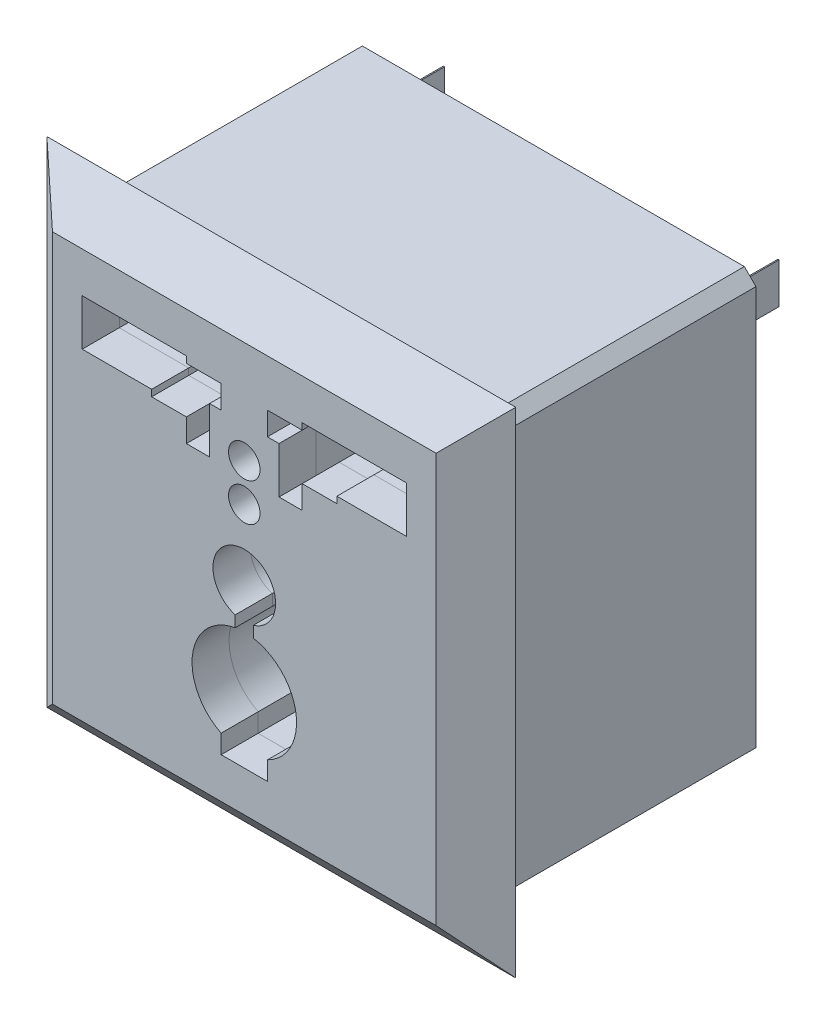
SolidWorks part; units mm, degrees
ref_plane "Front Plane" through (0, 0, 0) normal (0, 0, 1) x (1, 0, 0)
ref_plane "Top Plane" through (0, 0, 0) normal (0, 1, 0) x (1, 0, 0)
ref_plane "Right Plane" through (0, 0, 0) normal (1, 0, 0) x (0, 0, -1)
sketch "Sketch1" plane through (0, 0, 0) normal (0, 0, 1) x (1, 0, 0)
  line L1 (-20.25, 21.35) -> (20.25, 21.35)
  line L2 (-20.25, 21.35) -> (-20.25, -21.35)
  line L3 (-20.25, -21.35) -> (20.25, -21.35)
  line L4 (20.25, 21.35) -> (20.25, -21.35)
  line L5 (-20.25, 21.35) -> (20.25, -21.35) construction
  line L6 (-20.25, -21.35) -> (20.25, 21.35) construction
  point P0 (0, 0)
  dimension "D1" = 42.7
  dimension "D2" = 40.5
sketch "Sketch2" plane through (0, 0, 0) normal (0, 0, 1) x (1, 0, 0)
extrude "Boss-Extrude1" add sketch "Sketch1" along normal blind 3.2 draft 49 contours L1 L4 L3 L2
sketch "Sketch6" plane through (0, 0, 0) normal (0, 0, -1) x (-1, 0, 0)
  line L0 (0.05, -20) -> (-0.05, -20)
  line L1 (-17.5, 18.25) -> (17.5, 18.25)
  line L2 (-17.5, 18.25) -> (-17.5, -18.25)
  line L3 (-17.5, -18.25) -> (17.5, -18.25)
  line L4 (17.5, 18.25) -> (17.5, -18.25)
  line L5 (-17.5, 18.25) -> (17.5, -18.25) construction
  line L6 (-17.5, -18.25) -> (17.5, 18.25) construction
  line L7 (1.75, -14.5256) -> (-1.75, -14.5256)
  line L8 (1.75, -14.5256) -> (1.75, -14.4256)
  line L9 (1.75, -14.4256) -> (-1.75, -14.4256)
  line L10 (-1.75, -14.5256) -> (-1.75, -14.4256)
  line L11 (1.75, -14.5256) -> (-1.75, -14.4256) construction
  line L12 (1.75, -14.4256) -> (-1.75, -14.5256) construction
  line L17 (0.05, -20) -> (0.05, -16.5)
  line L18 (0.05, -16.5) -> (-0.05, -16.5)
  line L19 (14.5, 11.75) -> (14.4, 11.75)
  line L20 (14.5, 11.75) -> (14.5, 15.25)
  line L21 (14.5, 15.25) -> (14.4, 15.25)
  line L22 (14.4, 11.75) -> (14.4, 15.25)
  line L23 (14.5, 11.75) -> (14.4, 15.25) construction
  line L24 (14.5, 15.25) -> (14.4, 11.75) construction
  line L25 (-0.05, -20) -> (-0.05, -16.5)
  point P0 (0, 0)
  point P6 (0, -14.4756)
  point P16 (14.45, 13.5)
  dimension "D1" = 36.5
  dimension "D2" = 35
  dimension "D3" = 3.5
  dimension "D4" = 0.1
  dimension "D5" = 17.5
  dimension "D9" = 3.5
  dimension "D10" = 0.1
  dimension "D11" = 3
  dimension "D12" = 3
extrude "Boss-Extrude2" add sketch "Sketch6" along normal blind 23.5 contours L2 L1 L4 L3
sketch "Sketch7" plane through (0, 0, -23.5) normal (0, 0, -1) x (-1, 0, 0)
  line L0 (-17.5, 18.25) -> (-16.5, 18.25)
  line L1 (-16.5, 18.25) -> (-17.5, 17.25)
  line L2 (-17.5, 17.25) -> (-17.5, 18.25)
  line L3 (-17.5, 18.25) -> (17.5, 18.25) construction
  line L4 (-17.5, 18.25) -> (-17.5, -18.25) construction
  line L5 (17.5, 18.25) -> (17.5, 17.25)
  line L6 (17.5, 18.25) -> (17.5, -18.25) construction
  line L7 (17.5, 17.25) -> (16.5, 18.25)
  line L8 (16.5, 18.25) -> (17.5, 18.25)
  line L9 (17.5, -18.25) -> (17.5, -17.25)
  line L10 (17.5, -17.25) -> (16.5, -18.25)
  line L11 (-17.5, -18.25) -> (17.5, -18.25) construction
  line L12 (16.5, -18.25) -> (17.5, -18.25)
  line L13 (-17.5, -18.25) -> (-16.5, -18.25)
  line L14 (-16.5, -18.25) -> (-17.5, -17.25)
  line L15 (-17.5, -17.25) -> (-17.5, -18.25)
  dimension "D1" = 1
  dimension "D2" = 1
  dimension "D3" = 1
  dimension "D4" = 1
  dimension "D5" = 1
  dimension "D6" = 1
  dimension "D7" = 1
  dimension "D8" = 1
sketch "Sketch10" plane through (0, 0, -23.5) normal (0, 0, -1) x (-1, 0, 0)
sketch "Sketch11" plane through (0, 0, -23.5) normal (0, 0, -1) x (-1, 0, 0)
sketch "Sketch9" plane through (0, 0, 3.2) normal (0, 0, 1) x (1, 0, 0)
  line L0 (-16.5688, -17.6688) -> (16.5688, -17.6688) construction
  line L1 (2.0012, -14.1688) -> (-1.9988, -14.1688)
  line L2 (2.0012, -14.1688) -> (2.0012, -8.507)
  line L3 (2.0012, -8.507) -> (-1.9988, -8.507)
  line L4 (-1.9988, -14.1688) -> (-1.9988, -8.507)
  line L5 (2.0012, -14.1688) -> (-1.9988, -8.507) construction
  line L6 (2.0012, -8.507) -> (-1.9988, -14.1688) construction
  line L7 (0.7841, -5.6938) -> (-0.7817, -5.6938)
  line L8 (0.7841, -5.6938) -> (0.7841, -2.2911)
  line L9 (0.7841, -2.2911) -> (-0.7817, -2.2911)
  line L10 (-0.7817, -5.6938) -> (-0.7817, -2.2911)
  line L11 (0.7841, -5.6938) -> (-0.7817, -2.2911) construction
  line L12 (0.7841, -2.2911) -> (-0.7817, -5.6938) construction
  line L13 (-3, 7.6044) -> (-5, 7.6044)
  line L14 (-3, 7.6044) -> (-3, 11.6044)
  line L15 (-3, 11.6044) -> (-5, 11.6044)
  line L16 (-5, 7.6044) -> (-5, 11.6044)
  line L17 (-5, 11.6044) -> (-2, 11.6044)
  line L18 (-5, 11.6044) -> (-5, 13.6044)
  line L19 (-5, 13.6044) -> (-2, 13.6044)
  line L20 (-2, 11.6044) -> (-2, 13.6044)
  line L21 (-5, 9.6044) -> (-8, 9.6044)
  line L22 (-5, 9.6044) -> (-5, 11.6044)
  line L23 (-5, 11.6044) -> (-8, 11.6044)
  line L24 (-8, 9.6044) -> (-8, 11.6044)
  line L25 (-5, 10.1688) -> (-14, 10.1688)
  line L26 (-5, 10.1688) -> (-5, 14.1688)
  line L27 (-5, 14.1688) -> (-14, 14.1688)
  line L28 (-14, 10.1688) -> (-14, 14.1688)
  line L29 (-16.5688, 17.6688) -> (16.5688, 17.6688) construction
  line L62 (-16.5688, 17.6688) -> (-16.5688, -17.6688) construction
  line L63 (14, 10.1688) -> (5, 10.1688)
  line L64 (14, 10.1688) -> (14, 14.1688)
  line L65 (14, 14.1688) -> (5, 14.1688)
  line L66 (5, 10.1688) -> (5, 14.1688)
  line L67 (2, 11.6088) -> (5, 11.6088)
  line L68 (2, 11.6088) -> (2, 13.6088)
  line L69 (2, 13.6088) -> (5, 13.6088)
  line L70 (5, 11.6088) -> (5, 13.6088)
  line L71 (5, 7.6088) -> (3, 7.6088)
  line L72 (5, 7.6088) -> (5, 11.6088)
  line L73 (5, 11.6088) -> (3, 11.6088)
  line L74 (3, 7.6088) -> (3, 11.6088)
  line L75 (8, 9.6088) -> (5, 9.6088)
  line L76 (8, 9.6088) -> (8, 11.6088)
  line L77 (8, 11.6088) -> (5, 11.6088)
  line L78 (5, 9.6088) -> (5, 11.6088)
  line L79 (16.5688, 17.6688) -> (16.5688, -17.6688) construction
  circle A0 centre (0.0012, -8.507) radius 4.5146
  circle A1 centre (0.0012, -0.5054) radius 2.7059
  circle A2 centre (0, 5.5548) radius 1.36
  circle A3 centre (0, 8.8223) radius 1.36
  point P0 (0.0012, -11.3379)
  point P5 (0.0012, -3.9924)
  point P34 (0, -17.6688)
  point P61 (0.0012, -2.2911)
  dimension "D28" = 9.0292
  dimension "D30" = 5.4118
  dimension "D31" = 2.72
  dimension "D32" = 2.72
  dimension "D1" = 3.5
  dimension "D2" = 3.5
  dimension "D3" = 3
  dimension "D4" = 6
  dimension "D5" = 12
  dimension "D6" = 2
  dimension "D7" = 3.5
  dimension "D8" = 0.56
  dimension "D9" = 2
  dimension "D10" = 2
  dimension "D11" = 9
  dimension "D12" = 16.5688
  dimension "D13" = 2
  dimension "D14" = 4
  dimension "D15" = 4
  dimension "D16" = 2
  dimension "D17" = 12
  dimension "D18" = 4
  dimension "D19" = 2
  dimension "D20" = 3
  dimension "D21" = 0.5644
  dimension "D22" = 5
  dimension "D23" = 16.57
  dimension "D24" = 4
  dimension "D25" = 5.6618
  dimension "D26" = 16.57
  dimension "D27" = 1.5658
  dimension "D29" = 3.4027
  dimension "D33" = 6.0602
  dimension "D34" = 3.2675
  dimension "D35" = 4
  dimension "D36" = 2
  dimension "D37" = 1.7856
  dimension "D38" = 16.5688
  dimension "D39" = 2
  dimension "D40" = 3
  dimension "D41" = 2
  dimension "D42" = 3
extrude "Cut-Extrude9" cut sketch "Sketch7" against normal up to next (23.5 mm away)
sketch "Sketch13" plane through (0, 0, -23.5) normal (0, 0, -1) x (-1, 0, 0)
  line L12 (-16.5, 18.25) -> (16.5, 18.25) construction
  line L13 (-14.5, 15.25) -> (-14.4, 15.25)
  line L17 (-14.5, 15.25) -> (-14.5, 11.75)
  line L18 (-14.5, 11.75) -> (-14.4, 11.75)
  line L19 (-14.4, 15.25) -> (-14.4, 11.75)
  line L20 (-14.5, 15.25) -> (-14.4, 11.75) construction
  line L21 (-14.5, 11.75) -> (-14.4, 15.25) construction
  line L22 (-17.5, 17.25) -> (-17.5, -17.25) construction
  line L23 (14.4, 15.25) -> (14.5, 15.25)
  line L24 (14.4, 15.25) -> (14.4, 11.75)
  line L25 (14.4, 11.75) -> (14.5, 11.75)
  line L26 (14.5, 15.25) -> (14.5, 11.75)
  line L27 (17.5, 17.25) -> (17.5, -17.25) construction
  line L32 (-16.5, -18.25) -> (16.5, -18.25) construction
  line L33 (-1.75, -15.15) -> (1.75, -15.15)
  line L34 (-1.75, -15.15) -> (-1.75, -15.25)
  line L35 (-1.75, -15.25) -> (1.75, -15.25)
  line L36 (1.75, -15.15) -> (1.75, -15.25)
  line L37 (-1.75, -15.15) -> (1.75, -15.25) construction
  line L38 (-1.75, -15.25) -> (1.75, -15.15) construction
  point P0 (-14.45, 13.5)
  point P7 (0, -15.2)
  dimension "D1" = 3.5
  dimension "D2" = 0.1
  dimension "D3" = 3
  dimension "D4" = 3
  dimension "D5" = 0.1
  dimension "D6" = 3.5
  dimension "D7" = 3
  dimension "D8" = 3
  dimension "D9" = 0.1
  dimension "D10" = 3.5
  dimension "D11" = 3
  dimension "D12" = 17.5
extrude "Boss-Extrude3" add sketch "Sketch13" along normal blind 5
extrude "Cut-Extrude12" cut sketch "Sketch9" against normal blind 15 contours L28 L25 L24 L23 L18 L26 L27 | L16 L25 L24 L21 | L16 L13 L14 L15 L22 | L17 L20 L19 L18 L15 | A3 | A2 | L74 L71 L72 L66 L67 | L69 L68 L67 L66 | L76 L77 L66 L63 | L75 L76 L63 L72 | L77 L76 L63 L64 L65 L66 | L25 L22 L23 L24 | L8 A1 L10 L9 | L10 A1 L8 L9 | A1 L10 A0 L8 | L8 A0 L10 L7 | L10 A0 L4 L3 L2 L8 L7 | L4 A0 L2 L3 | A0 L4 L1 L2
